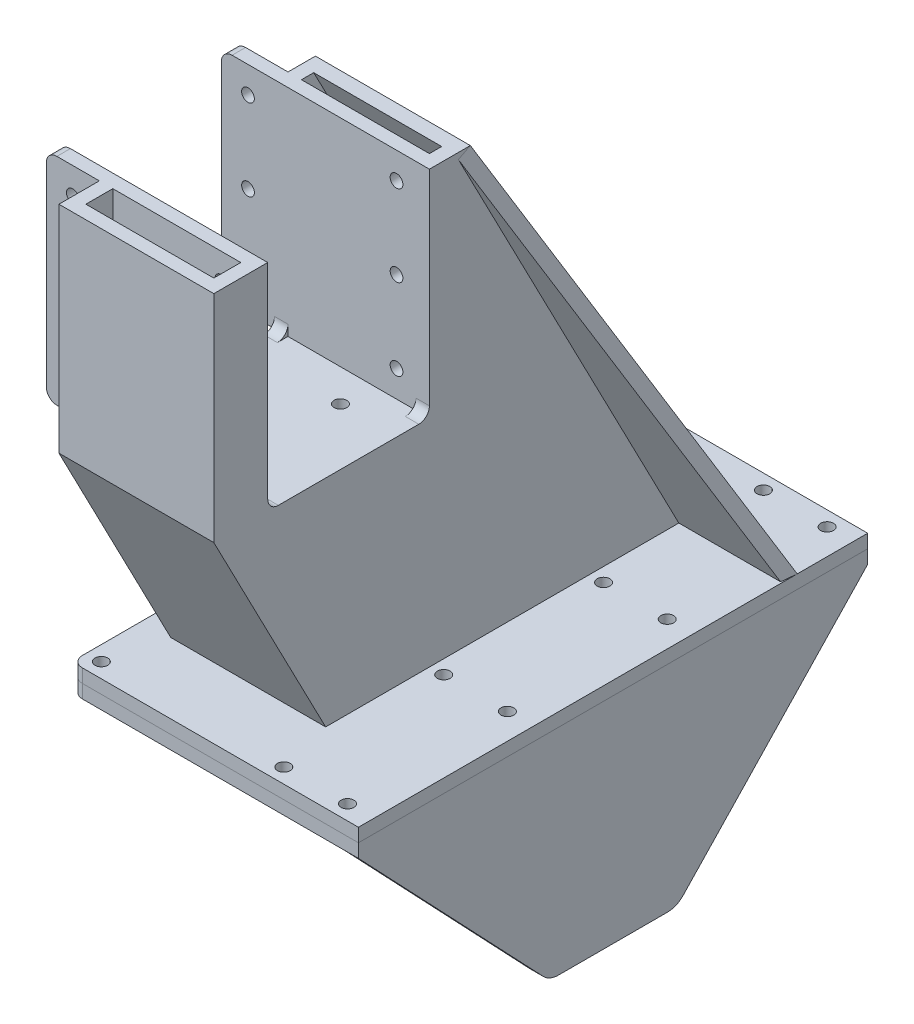
SolidWorks part; units mm, degrees
ref_plane "Front Plane" through (0, 0, 0) normal (0, 0, 1) x (1, 0, 0)
ref_plane "Top Plane" through (0, 0, 0) normal (0, 1, 0) x (1, 0, 0)
ref_plane "Right Plane" through (0, 0, 0) normal (1, 0, 0) x (0, 0, -1)
sketch "Sketch1" plane through (0, 0, 0) normal (1, 0, 0) x (0, 0, -1)
  line L0 (-239.7522, 215.8869) -> (-118.8684, 215.8869)
  line L1 (-118.8684, 215.8869) -> (-13.4575, 12.6869)
  line L2 (-13.4575, 12.6869) -> (-187.0468, 12.6869)
  line L3 (-187.0468, 12.6869) -> (-239.7522, 114.2869)
  line L4 (-239.7522, 114.2869) -> (-239.7522, 215.8869)
  dimension "D1" = 203.2
  dimension "D2" = 101.6
  dimension "D3" = 173.5893
extrude "Boss-Extrude1" add sketch "Sketch1" against normal blind 73 from offset 40
shell "Shell1" thickness 6.35
sketch "Sketch4" plane through (0, 12.6869, 0) normal (0, -1, 0) x (1, 0, 0)
  line L0 (53.5, 220.2522) -> (-46.5, -19.7478) construction
  line L1 (-46.5, 220.2522) -> (53.5, 220.2522)
  line L2 (-46.5, 220.2522) -> (-46.5, -19.7478)
  line L3 (-46.5, -19.7478) -> (53.5, -19.7478)
  line L4 (53.5, 220.2522) -> (53.5, -19.7478)
  line L5 (-33, 187.0468) -> (40, 13.4575) construction
  line L10 (-39.5, 213.2522) -> (-39.5, -12.7478) construction
  line L11 (-39.5, -12.7478) -> (46.5, -12.7478) construction
  line L13 (-39.5, 213.2522) -> (46.5, 213.2522) construction
  line L14 (46.5, 137.9188) -> (-39.5, 137.9188) construction
  line L15 (3.5, 100.2522) -> (53.5, 100.2522) construction
  line L16 (46.5, 213.2522) -> (46.5, 137.9188) construction
  line L17 (46.5, 213.2522) -> (46.5, -12.7478) construction
  line L18 (46.5, 137.9188) -> (46.5, 62.5855) construction
  line L19 (46.5, 62.5855) -> (46.5, -12.7478) construction
  line L20 (-33, 187.0468) -> (40, 187.0468) construction
  line L21 (-33, 187.0468) -> (-33, 13.4575) construction
  circle A0 centre (46.5, 213.2522) radius 3
  circle A1 centre (-39.5, 213.2522) radius 3
  circle A2 centre (46.5, 137.9188) radius 3
  circle A3 centre (-39.5, 137.9188) radius 3
  circle A4 centre (46.5, 62.5855) radius 3
  circle A5 centre (46.5, -12.7478) radius 3
  circle A6 centre (-39.5, -12.7478) radius 3
  circle A7 centre (-39.5, 62.5855) radius 3
  point P4 (3.5, 100.2522)
  dimension "D5" = 6
  dimension "D1" = 100
  dimension "D2" = 240
  dimension "D3" = 7
extrude "Boss-Extrude2" add sketch "Sketch4" along normal blind 6.35 separate body
fillet "Fillet1" radius 5 2 edges at (-46.5, 9.5119, 220.2522) (-46.5, 9.5119, -19.7478)
sketch "Sketch5" plane through (0, 0, 0) normal (1, 0, 0) x (0, 0, -1)
  line L0 (-118.8684, 215.8869) -> (-239.7522, 215.8869) construction
  line L1 (-138.1522, 114.2869) -> (-214.3522, 114.2869)
  line L2 (-138.1522, 114.2869) -> (-138.1522, 215.8869)
  line L3 (-138.1522, 215.8869) -> (-214.3522, 215.8869)
  line L4 (-214.3522, 114.2869) -> (-214.3522, 215.8869)
  line L5 (-138.1522, 114.2869) -> (-214.3522, 215.8869) construction
  line L6 (-138.1522, 215.8869) -> (-214.3522, 114.2869) construction
  line L7 (-239.7522, 215.8869) -> (-239.7522, 114.2869) construction
  point P0 (-176.2522, 165.0869)
  dimension "D1" = 76.2
  dimension "D2" = 101.6
  dimension "D3" = 25.4
extrude "Cut-Extrude2" cut sketch "Sketch5" against normal through all both and the other way through all
fillet "Fillet2" radius 5 4 edges at (36.825, 114.2869, 214.3522) (36.825, 114.2869, 138.1522) (-29.825, 114.2869, 138.1522) (-29.825, 114.2869, 214.3522)
mirror "Mirror1" about plane through (0, 6.3369, 0) normal (0, -1, 0) of bodies 103
sketch "Sketch10" plane through (0, -0.0131, 0) normal (0, -1, 0) x (1, 0, 0)
  line L0 (-21.5, 100.2522) -> (-46.5, 100.2522) construction
  line L1 (-46.5, 220.2522) -> (53.5, 220.2522) construction
  line L2 (-46.5, 220.2522) -> (-46.5, -19.7478) construction
  line L3 (-46.5, -19.7478) -> (53.5, -19.7478) construction
  line L4 (53.5, 220.2522) -> (53.5, -19.7478) construction
  line L6 (-46.5, 215.2522) -> (-46.5, -14.7478) construction
  line L7 (53.5, 220.2522) -> (-41.5, 220.2522) construction
  line L8 (-41.5, -19.7478) -> (53.5, -19.7478) construction
  line L9 (-16.5, 175.2522) -> (23.5, 175.2522)
  line L10 (28.5, 170.2522) -> (28.5, 30.2522)
  line L11 (-16.5, 25.2522) -> (23.5, 25.2522)
  line L12 (-21.5, 170.2522) -> (-21.5, 30.2522)
  line L13 (28.5, 100.2522) -> (53.5, 100.2522) construction
  arc A0 (28.5, 30.2522) -> (23.5, 25.2522) centre (23.5, 30.2522) cw
  arc A1 (-16.5, 25.2522) -> (-21.5, 30.2522) centre (-16.5, 30.2522) cw
  arc A2 (-16.5, 175.2522) -> (-21.5, 170.2522) centre (-16.5, 170.2522) ccw
  arc A3 (23.5, 175.2522) -> (28.5, 170.2522) centre (23.5, 170.2522) cw
  dimension "D2" = 5
  dimension "D1" = 150
  dimension "D3" = 50
extrude "Cut-Extrude4" cut sketch "Sketch10" against normal blind 45.35
combine bodies "Combine1" operation type add bodies to combine 109 104
sketch "Sketch11" plane through (40, 0, 0) normal (1, 0, 0) x (0, 0, -1)
  line L1 (-214.3522, 215.8869) -> (-220.7022, 215.8869)
  line L2 (-214.3522, 215.8869) -> (-214.3522, 114.2869)
  line L3 (-214.3522, 114.2869) -> (-220.7022, 114.2869)
  line L4 (-220.7022, 215.8869) -> (-220.7022, 114.2869)
  line L5 (-138.1522, 215.8869) -> (-131.8022, 215.8869)
  line L6 (-138.1522, 215.8869) -> (-138.1522, 114.2869)
  line L7 (-138.1522, 114.2869) -> (-131.8022, 114.2869)
  line L8 (-131.8022, 215.8869) -> (-131.8022, 114.2869)
  line L9 (-143.1522, 114.2869) -> (-209.3522, 114.2869) construction
  dimension "D1" = 6.35
extrude "Boss-Extrude4" add sketch "Sketch11" against normal blind 98
sketch "Sketch12" plane through (40, 0, 0) normal (1, 0, 0) x (0, 0, -1)
  line L1 (-220.7022, 114.2869) -> (-131.8022, 114.2869)
  line L2 (-220.7022, 114.2869) -> (-220.7022, 107.9369)
  line L3 (-220.7022, 107.9369) -> (-131.8022, 107.9369)
  line L4 (-131.8022, 114.2869) -> (-131.8022, 107.9369)
  line L6 (-143.1522, 114.2869) -> (-209.3522, 114.2869) construction
  line L7 (-214.3522, 119.2869) -> (-214.3522, 215.8869) construction
  line L8 (-138.1522, 215.8869) -> (-138.1522, 119.2869) construction
  dimension "D1" = 6.35
  dimension "D2" = 6.35
  dimension "D3" = 6.35
extrude "Boss-Extrude6" add sketch "Sketch12" against normal up to surface (66.65 mm away) up to face at (-26.65, 128.4654, 170.3902)
sketch "Sketch13" plane through (0, 0, 131.8022) normal (0, 0, -1) x (-1, 0, 0)
  line L0 (45.5, 215.8869) -> (45.5, 203.3869) construction
  line L1 (58, 215.8869) -> (33, 215.8869) construction
  line L2 (45.5, 203.3869) -> (45.5, 165.0869) construction
  line L3 (45.5, 165.0869) -> (45.5, 126.7869) construction
  line L4 (45.5, 126.7869) -> (45.5, 114.2869) construction
  line L5 (58, 114.2869) -> (33, 114.2869) construction
  line L6 (45.5, 203.3869) -> (58, 203.3869) construction
  line L7 (58, 114.2869) -> (58, 215.8869) construction
  line L8 (10.5, 215.8869) -> (10.5, 114.2869) construction
  line L9 (33, 215.8869) -> (-40, 215.8869) construction
  line L10 (10.5, 114.2869) -> (33, 114.2869) construction
  line L11 (33, 12.6869) -> (33, 215.8869) construction
  circle A0 centre (45.5, 203.3869) radius 3
  circle A1 centre (45.5, 165.0869) radius 3
  circle A2 centre (45.5, 126.7869) radius 3
  circle A3 centre (-24.5, 126.7869) radius 3
  circle A4 centre (-24.5, 165.0869) radius 3
  circle A5 centre (-24.5, 203.3869) radius 3
  dimension "D1" = 6
  dimension "D2" = 70
extrude "Cut-Extrude5" cut sketch "Sketch13" along direction (0, 0, 1) on the side against the normal up to surface (88.9 mm away)
fillet "Fillet5" radius 5 4 edges at (-58, 114.2869, 134.9772) (-58, 114.2869, 217.5272) (-58, 215.8869, 134.9772) (-58, 215.8869, 217.5272)
sketch "Sketch14" plane through (0, 114.2869, 0) normal (0, 1, 0) x (1, 0, 0)
  line L0 (13.268, -138.1522) -> (13.268, -153.35) construction
  line L1 (-26.65, -138.1522) -> (33.65, -138.1522) construction
  line L2 (13.268, -153.35) -> (13.268, -199.1545) construction
  line L3 (13.268, -199.1545) -> (13.268, -214.3522) construction
  line L4 (-26.65, -214.3522) -> (33.65, -214.3522) construction
  circle A0 centre (13.268, -153.35) radius 3
  circle A1 centre (13.268, -199.1545) radius 3
  dimension "D1" = 6
extrude "Cut-Extrude6" cut sketch "Sketch14" against normal blind 14
sketch "Sketch15" plane through (0, 0, -19.7478) normal (0, 0, -1) x (-1, 0, 0)
  line L0 (-53.5, -0.0131) -> (-82.3, -0.0131)
  line L1 (-82.3, -0.0131) -> (-82.3, -94.8131)
  line L2 (-82.3, -94.8131) -> (-88.65, -94.8131)
  line L3 (-88.65, -94.8131) -> (-88.65, 6.3369)
  line L4 (-88.65, 6.3369) -> (-53.5, 6.3369)
  line L5 (-53.5, 6.3369) -> (-53.5, -0.0131)
  dimension "D1" = 28.8
  dimension "D2" = 6.35
  dimension "D3" = 101.15
extrude "Boss-Extrude7" add sketch "Sketch15" against normal up to surface (240 mm away) up to face at (6, 3.1619, 220.2522)
sketch "Sketch16" plane through (82.3, 0, 0) normal (-1, 0, 0) x (0, 0, 1)
  line L0 (100.2522, -94.8131) -> (100.2522, -0.0131) construction
  line L1 (220.2522, -94.8131) -> (-19.7478, -94.8131) construction
  line L2 (215.2522, -0.0131) -> (-14.7478, -0.0131) construction
  line L3 (-19.7478, -0.0131) -> (70.2522, -94.8131)
  line L4 (70.2522, -94.8131) -> (130.2522, -94.8131)
  line L5 (130.2522, -94.8131) -> (220.2522, -0.0131)
  line L6 (220.2522, -0.0131) -> (220.2522, -200.0131)
  line L7 (220.2522, -200.0131) -> (-19.7478, -200.0131)
  line L8 (-19.7478, -200.0131) -> (-19.7478, -0.0131)
  point P9 (0, 0)
  point P15 (-19.7478, -0.0131)
  point P17 (220.2522, -0.0131)
  dimension "D1" = 60
  dimension "D2" = 200
extrude "Cut-Extrude7" cut sketch "Sketch16" against normal through all
fillet "Fillet6" radius 10 2 edges at (85.475, -94.8131, 130.2522) (85.475, -94.8131, 70.2522)
sketch "Sketch17" plane through (0, 6.3369, 0) normal (0, 1, 0) x (1, 0, 0)
  line L1 (88.65, 19.7478) -> (53.5, 19.7478)
  line L2 (88.65, 19.7478) -> (88.65, -220.2522)
  line L3 (88.65, -220.2522) -> (53.5, -220.2522)
  line L4 (53.5, 19.7478) -> (53.5, -220.2522)
extrude "Boss-Extrude8" add sketch "Sketch17" along normal up to vertex
sketch "Sketch18" plane through (0, 12.6869, 0) normal (0, 1, 0) x (1, 0, 0)
  line L0 (46.5, 12.7478) -> (46.5, -62.5855) construction
  line L1 (46.5, -62.5855) -> (46.5, -137.9188) construction
  line L2 (46.5, -137.9188) -> (46.5, -213.2522) construction
  line L3 (76.5, 12.7478) -> (76.5, -62.5855) construction
  line L4 (76.5, -62.5855) -> (76.5, -137.9188) construction
  line L5 (76.5, -137.9188) -> (76.5, -213.2522) construction
  circle A0 centre (76.5, 12.7478) radius 3
  circle A1 centre (76.5, -62.5855) radius 3
  circle A2 centre (76.5, -137.9188) radius 3
  circle A3 centre (76.5, -213.2522) radius 3
  circle A4 centre (46.5, 12.7478) radius 3 construction
  dimension "D2" = 30
  dimension "D1" = 2
extrude "Cut-Extrude8" cut sketch "Sketch18" against normal through all
sketch "Sketch19" plane through (0, -2.8107, 5.4181) normal (0, 0.4605, -0.8877) x (-1, 0, 0)
  line L0 (-40, 246.3729) -> (-88.65, 17.4587)
  line L1 (-88.65, 17.4587) -> (-40, 17.4587)
  line L2 (-40, 17.4587) -> (-40, 246.3729) construction
  line L3 (-40, 17.4587) -> (-40, 246.3729)
  line L4 (-88.65, 112.6839) -> (-88.65, 2.1682) construction
  line L5 (33, 17.4587) -> (-40, 17.4587) construction
  point P3 (-88.65, 17.202)
  point P9 (-40, 246.3729)
  point P10 (-40, 20.7501)
extrude "Boss-Extrude9" add sketch "Sketch19" against normal blind 6.35
mirror "Mirror2" [suppressed] about plane through (0, 0, 0) normal (1, 0, 0)
delete or keep bodies "Body-Delete/Keep 1" [suppressed] type delete bodies bodies 108 110
